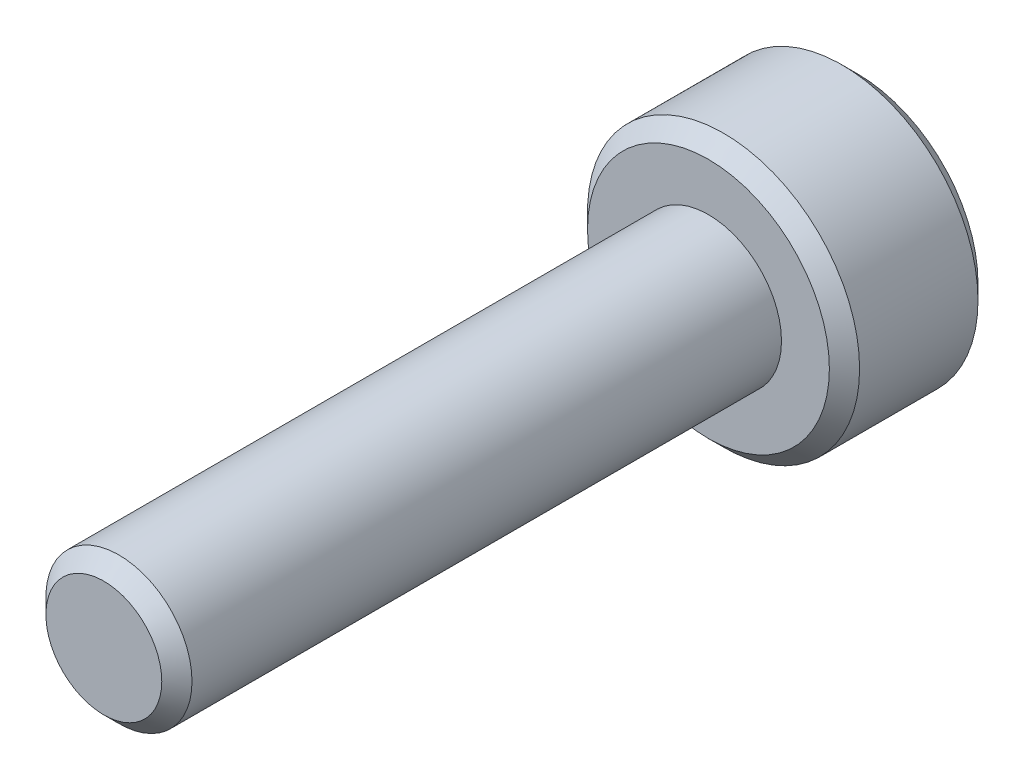
SolidWorks part; units mm, degrees
material "AISI 1020"
ref_plane "Front" through (0, 0, 0) normal (0, 0, 1) x (1, 0, 0)
ref_plane "Top" through (0, 0, 0) normal (0, 1, 0) x (1, 0, 0)
ref_plane "Right" through (0, 0, 0) normal (1, 0, 0) x (0, 0, -1)
sketch "Skizze1" plane through (0, 0, 0) normal (0, 0, 1) x (1, 0, 0)
  circle A0 centre (0, 0) radius 2.7
  dimension "D1" = 5.4
extrude "Aufsatz-Linear austragen1" add sketch "Skizze1" along normal blind 2.95
sketch "Skizze2" plane through (0, 0, 2.95) normal (0, 0, 1) x (1, 0, 0)
  circle A0 centre (0, 0) radius 1.45
  dimension "D1" = 2.9
extrude "Aufsatz-Linear austragen2" add sketch "Skizze2" along normal blind 12
chamfer "Fase1" distance 0.3 angle 45 3 edges at (2.7, 0, 2.95) (2.7, 0, 0) (1.45, 0, 14.95)
sketch "Skizze3" plane through (0, 0, 0) normal (0, 0, -1) x (-1, 0, 0)
  line L0 (1.25, 0) -> (0, 0) construction
  line L1 (1.25, 0.7217) -> (0, 1.4434)
  line L2 (0, 1.4434) -> (-1.25, 0.7217)
  line L3 (-1.25, 0.7217) -> (-1.25, -0.7217)
  line L4 (-1.25, -0.7217) -> (0, -1.4434)
  line L5 (0, -1.4434) -> (1.25, -0.7217)
  line L6 (1.25, -0.7217) -> (1.25, 0.7217)
  circle A0 centre (0, 0) radius 1.25 construction
  dimension "D1" = 2.5
extrude "Schnitt-Linear austragen1" cut sketch "Skizze3" against normal blind 2.5
